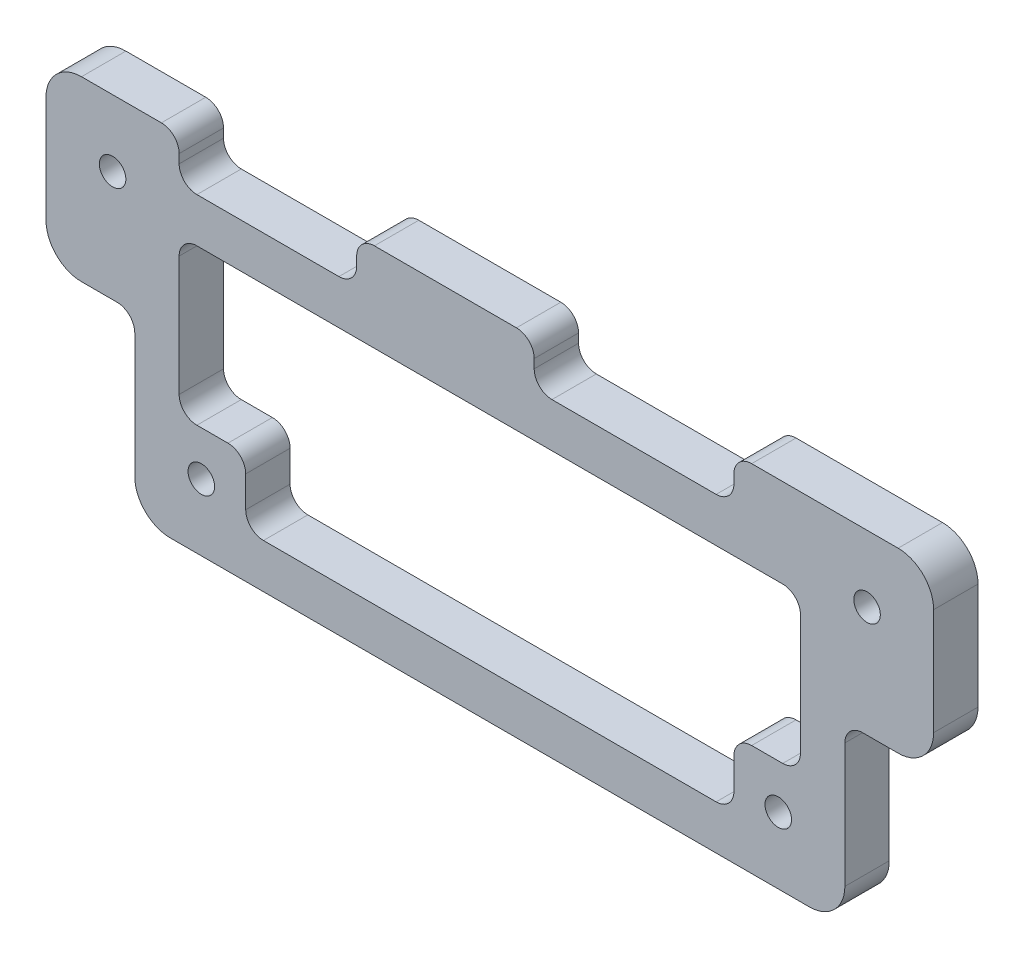
SolidWorks part; units mm, degrees
ref_plane "Front Plane" through (0, 0, 0) normal (0, 0, 1) x (1, 0, 0)
ref_plane "Top Plane" through (0, 0, 0) normal (0, 1, 0) x (1, 0, 0)
ref_plane "Right Plane" through (0, 0, 0) normal (1, 0, 0) x (0, 0, -1)
sketch "Sketch1" plane through (0, 0, 0) normal (0, 0, 1) x (1, 0, 0)
  line L0 (0, 25.4) -> (12.7, 25.4)
  line L1 (0, 0) -> (127, 0)
  line L2 (0, 0) -> (0, 50.8)
  line L3 (0, 50.8) -> (127, 50.8)
  line L4 (127, 0) -> (127, 50.8)
  line L5 (12.7, 25.4) -> (12.7, 0)
  line L6 (127, 25.4) -> (114.3, 25.4)
  line L7 (114.3, 25.4) -> (114.3, 0)
  circle A0 centre (23.622, 47.625) radius 1.5875
  circle A1 centre (38.1, 47.625) radius 1.5875
  circle A2 centre (78.74, 47.625) radius 1.5875
  circle A3 centre (89.662, 47.625) radius 1.5875
  circle A4 centre (52.324, 30.734) radius 1.5875
  circle A5 centre (52.324, 19.558) radius 1.5875
  circle A6 centre (9.525, 41.275) radius 1.8986
  circle A7 centre (22.225, 9.525) radius 1.8986
  circle A8 centre (104.775, 9.525) radius 1.8987
  circle A9 centre (117.475, 41.275) radius 1.8986
  dimension "D6" = 3.175
  dimension "D16" = 3.7973
  dimension "D1" = 127
  dimension "D2" = 50.8
  dimension "D3" = 12.7
  dimension "D4" = 12.7
  dimension "D5" = 25.4
  dimension "D7" = 14.478
  dimension "D8" = 10.922
  dimension "D9" = 3.175
  dimension "D10" = 3.175
  dimension "D11" = 20.066
  dimension "D12" = 11.176
  dimension "D13" = 38.1
  dimension "D14" = 48.26
  dimension "D15" = 52.324
  dimension "D17" = 9.525
  dimension "D18" = 9.525
  dimension "D19" = 9.525
  dimension "D20" = 9.525
  dimension "D21" = 9.525
  dimension "D22" = 9.525
  dimension "D23" = 9.525
  dimension "D24" = 9.525
extrude "Boss-Extrude1" add sketch "Sketch1" along normal blind 6.35 contours L7 L6 L4 L3 L2 L0 L5 L1 A9 A8 A7 A6 A5 A4 A3 A2 A1 A0
fillet "Fillet1" radius 5.08 6 edges at (0, 25.4, 3.175) (12.7, 0, 3.175) (114.3, 0, 3.175) (127, 25.4, 3.175) (127, 50.8, 3.175) (0, 50.8, 3.175)
fillet "Fillet2" radius 2.54 2 edges at (114.3, 25.4, 3.175) (12.7, 25.4, 3.175)
sketch "Sketch2" plane through (0, 0, 6.35) normal (0, 0, 1) x (1, 0, 0)
  line L8 (19.05, 50.8) -> (19.05, 44.45)
  line L9 (5.08, 50.8) -> (121.92, 50.8) construction
  line L10 (19.05, 44.45) -> (44.45, 44.45)
  line L11 (44.45, 44.45) -> (44.45, 50.8)
  line L12 (44.45, 50.8) -> (19.05, 50.8)
  line L13 (69.85, 50.8) -> (69.85, 44.45)
  line L14 (69.85, 44.45) -> (98.425, 44.45)
  line L15 (98.425, 44.45) -> (98.425, 50.8)
  line L16 (98.425, 50.8) -> (69.85, 50.8)
  line L17 (19.05, 38.1) -> (19.05, 15.875)
  line L18 (19.05, 15.875) -> (28.575, 15.875)
  line L19 (28.575, 15.875) -> (28.575, 6.35)
  line L20 (28.575, 6.35) -> (98.425, 6.35)
  line L21 (98.425, 6.35) -> (98.425, 15.875)
  line L22 (98.425, 15.875) -> (107.95, 15.875)
  line L23 (107.95, 15.875) -> (107.95, 38.1)
  line L24 (107.95, 38.1) -> (19.05, 38.1)
  line L25 (12.7, 22.86) -> (12.7, 5.08) construction
  line L26 (17.78, 0) -> (109.22, 0) construction
  line L27 (114.3, 22.86) -> (114.3, 5.08) construction
  dimension "D1" = 6.35
  dimension "D2" = 6.35
  dimension "D3" = 9.525
  dimension "D4" = 9.525
  dimension "D5" = 9.525
  dimension "D6" = 9.525
  dimension "D7" = 6.35
  dimension "D8" = 12.7
  dimension "D9" = 6.35
  dimension "D10" = 6.35
  dimension "D11" = 25.4
  dimension "D12" = 25.4
  dimension "D13" = 28.575
extrude "Cut-Extrude1" cut sketch "Sketch2" against normal blind 8.89
fillet "Fillet3" radius 2.54 16 edges at (28.575, 15.875, 3.175) (28.575, 6.35, 3.175) (98.425, 6.35, 3.175) (98.425, 15.875, 3.175) (107.95, 15.875, 3.175) (107.95, 38.1, 3.175) (19.05, 38.1, 3.175) (19.05, 15.875, 3.175) (98.425, 50.8, 3.175) (98.425, 44.45, 3.175) (69.85, 44.45, 3.175) (69.85, 50.8, 3.175) (44.45, 50.8, 3.175) (44.45, 44.45, 3.175) (19.05, 44.45, 3.175) (19.05, 50.8, 3.175)
